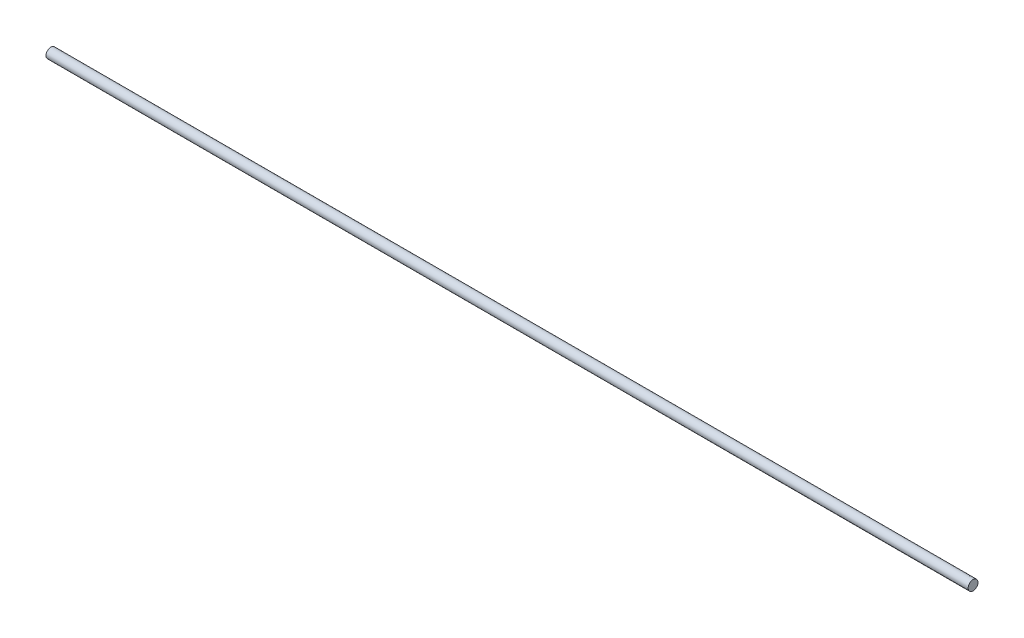
SolidWorks part; units mm, degrees
ref_plane "Front Plane" through (0, 0, 0) normal (0, 0, 1) x (1, 0, 0)
ref_plane "Top Plane" through (0, 0, 0) normal (0, 1, 0) x (1, 0, 0)
ref_plane "Right Plane" through (0, 0, 0) normal (1, 0, 0) x (0, 0, -1)
sketch "Sketch1" plane through (0, 0, 0) normal (1, 0, 0) x (0, 0, -1)
  circle A0 centre (0, 0) radius 4
  dimension "D1" = 8
extrude "Boss-Extrude1" add sketch "Sketch1" along normal blind 750 contours A0
